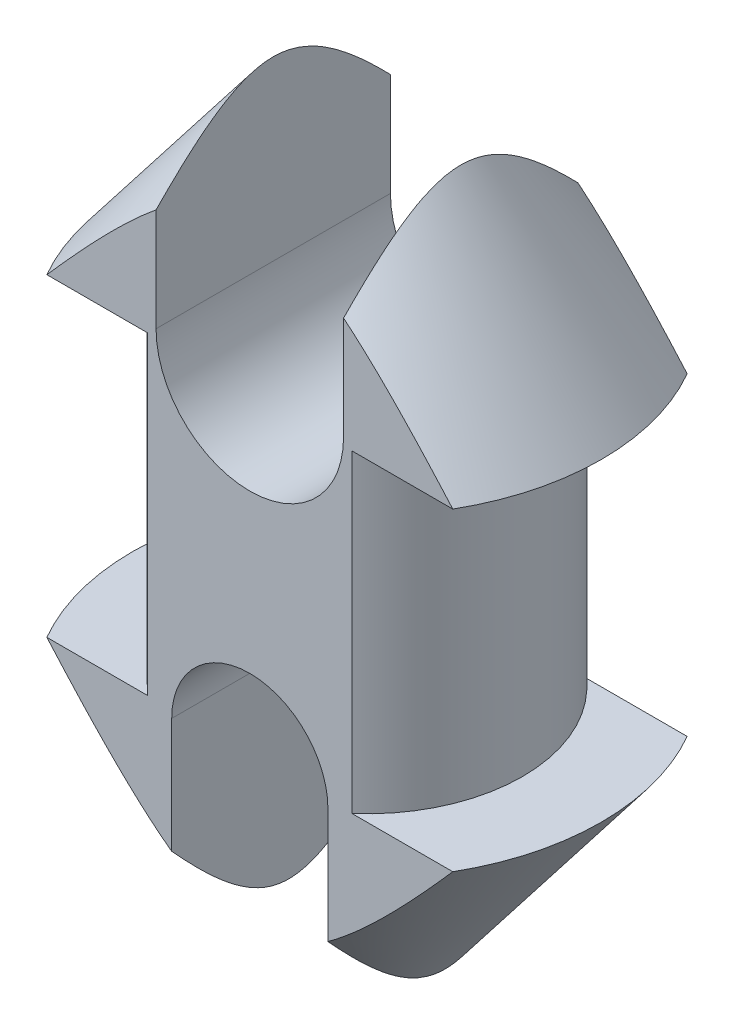
SolidWorks part; units mm, degrees
ref_plane "Plano frontal" through (0, 0, 0) normal (0, 0, 1) x (1, 0, 0)
ref_plane "Plano superior" through (0, 0, 0) normal (0, 1, 0) x (1, 0, 0)
ref_plane "Plano direito" through (0, 0, 0) normal (1, 0, 0) x (0, 0, -1)
sketch "Esboço1" plane through (0, 0, 0) normal (0, 0, 1) x (1, 0, 0)
  line L0 (0, -10.05) -> (0, 10.05) construction
  line L1 (-15, -10.05) -> (-15, 10.05)
  line L2 (15, -10.05) -> (15, 10.05)
  line L3 (15, 10.05) -> (9.95, 10.05)
  line L4 (9.95, 10.05) -> (9.95, -10.05)
  line L5 (9.95, -10.05) -> (15, -10.05)
  line L6 (0, 25.05) -> (0, -25.05)
  line L7 (0, -25.05) -> (0, 85.7647) construction
  line L8 (15, 10.05) -> (4, 24.5068)
  line L9 (15, -10.05) -> (4, -24.5068)
  arc A0 (-15, -10.05) -> (15, -10.05) centre (0, -10.05) ccw
  arc A1 (15, 10.05) -> (-15, 10.05) centre (0, 10.05) ccw
  point P2 (0, 0)
  dimension "D1" = 15
  dimension "D2" = 19.9
  dimension "D3" = 20.1
  dimension "D4" = 4
  dimension "D5" = 4
revolve "Revolução1" add sketch "Esboço1" angle 360 about L7
sketch "Esboço2" plane through (0, 0, 0) normal (0, 1, 0) x (1, 0, 0)
  line L1 (-15, -7.5) -> (15, -7.5)
  line L2 (-15, -7.5) -> (-15, 7.5)
  line L3 (-15, 7.5) -> (15, 7.5)
  line L4 (15, -7.5) -> (15, 7.5)
  line L5 (-15, -7.5) -> (15, 7.5) construction
  line L6 (-15, 7.5) -> (15, -7.5) construction
  circle A0 centre (0, 0) radius 15 construction
  point P0 (0, 0)
  dimension "D1" = 15
extrude "Corte-extrusão1" cut sketch "Esboço2" against normal through all both and the other way through all flip side to cut
sketch "Esboço3" plane through (0, 0, -7.5) normal (0, 0, -1) x (-1, 0, 0)
  line L0 (0, 25.05) -> (0, 10.55) construction
  line L1 (6, 25.05) -> (6, 10.55)
  line L2 (-6, 25.05) -> (-6, 10.55)
  line L3 (0, -25.05) -> (0, -10.55) construction
  line L4 (-5, -25.05) -> (-5, -10.55)
  line L5 (5, -25.05) -> (5, -10.55)
  arc A0 (4, 24.5068) -> (-4, 24.5068) centre (0, 10.05) ccw construction
  arc A1 (6, 25.05) -> (-6, 25.05) centre (0, 25.05) ccw
  arc A2 (-6, 10.55) -> (6, 10.55) centre (0, 10.55) ccw
  arc A3 (-4, -24.5068) -> (4, -24.5068) centre (0, -10.05) ccw construction
  arc A4 (-5, -25.05) -> (5, -25.05) centre (0, -25.05) ccw
  arc A5 (5, -10.55) -> (-5, -10.55) centre (0, -10.55) ccw
  point P6 (0, 17.8)
  point P11 (0, -17.8)
  dimension "D3" = 6
  dimension "D4" = 5
  dimension "D1" = 14.5
  dimension "D2" = 14.5
extrude "Corte-extrusão2" cut sketch "Esboço3" against normal through all
